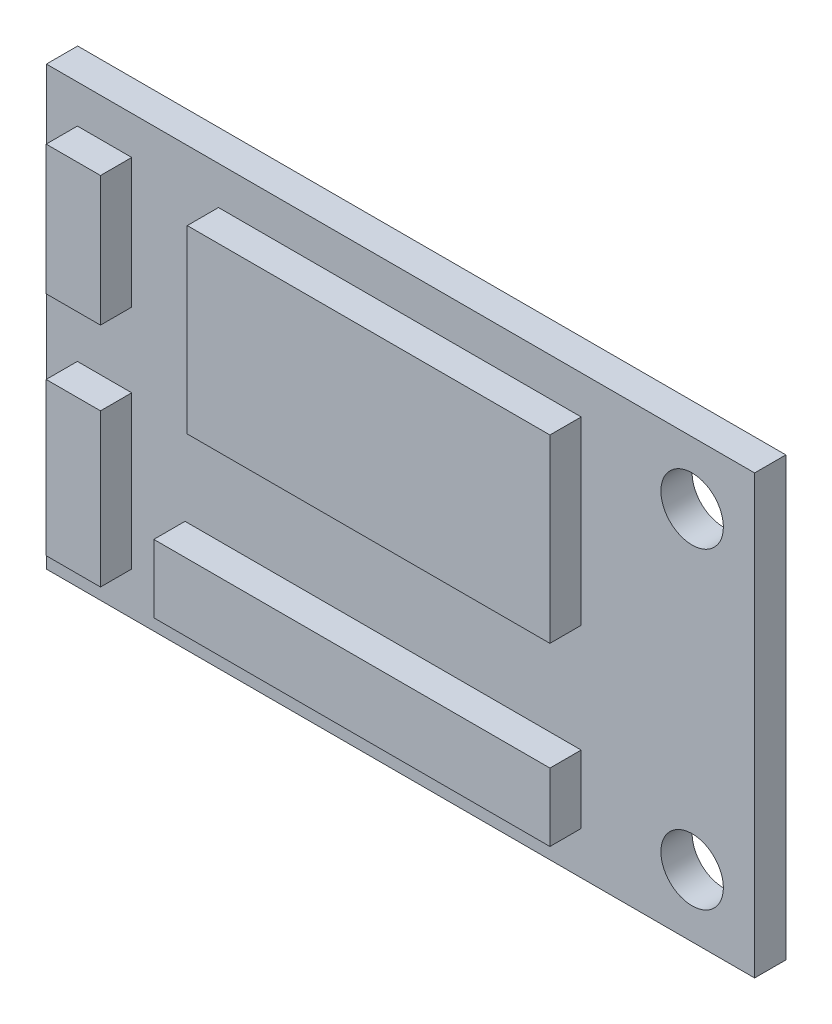
SolidWorks part; units mm, degrees
ref_plane "前视基准面" through (0, 0, 0) normal (0, 0, 1) x (1, 0, 0)
ref_plane "上视基准面" through (0, 0, 0) normal (0, 1, 0) x (1, 0, 0)
ref_plane "右视基准面" through (0, 0, 0) normal (1, 0, 0) x (0, 0, -1)
sketch "草图1" plane through (0, 0, 0) normal (0, 0, 1) x (1, 0, 0)
  line L0 (-50.883, 0) -> (36.1451, 0) construction
  line L1 (17, -10.5) -> (-17, -10.5)
  line L2 (17, -10.5) -> (17, 10.5)
  line L3 (17, 10.5) -> (-17, 10.5)
  line L4 (-17, -10.5) -> (-17, 10.5)
  line L5 (17, -10.5) -> (-17, 10.5) construction
  line L6 (17, 10.5) -> (-17, -10.5) construction
  line L7 (14, 14.5325) -> (14, -18.6521) construction
  circle A0 centre (14, 7.5) radius 1.5
  circle A1 centre (14, -7.5) radius 1.5
  point P0 (0, 0)
  dimension "D3" = 3
  dimension "D4" = 15
  dimension "D5" = 3
  dimension "D1" = 34
  dimension "D2" = 21
extrude "凸台-拉伸1" add sketch "草图1" along normal blind 1.5
sketch "草图2" plane through (0, 0, 1.5) normal (0, 0, 1) x (1, 0, 0)
  line L1 (-15.5131, 8.6645) -> (-12.9038, 8.6645)
  line L2 (-15.5131, 8.6645) -> (-15.5131, 2.4422)
  line L3 (-15.5131, 2.4422) -> (-12.9038, 2.4422)
  line L4 (-12.9038, 8.6645) -> (-12.9038, 2.4422)
  line L5 (-15.5131, -1.1205) -> (-12.9038, -1.1205)
  line L6 (-15.5131, -1.1205) -> (-15.5131, -8.4467)
  line L7 (-15.5131, -8.4467) -> (-12.9038, -8.4467)
  line L8 (-12.9038, -1.1205) -> (-12.9038, -8.4467)
  line L9 (-8.7389, 8.6645) -> (8.6734, 8.6645)
  line L10 (-8.7389, 8.6645) -> (-8.7389, 0)
  line L11 (-8.7389, 0) -> (8.6734, 0)
  line L12 (8.6734, 8.6645) -> (8.6734, 0)
  line L13 (-10.3447, -8.4467) -> (8.6734, -8.4467)
  line L14 (-10.3447, -8.4467) -> (-10.3447, -5.1851)
  line L15 (-10.3447, -5.1851) -> (8.6734, -5.1851)
  line L16 (8.6734, -8.4467) -> (8.6734, -5.1851)
extrude "凸台-拉伸2" add sketch "草图2" along normal blind 1.5
